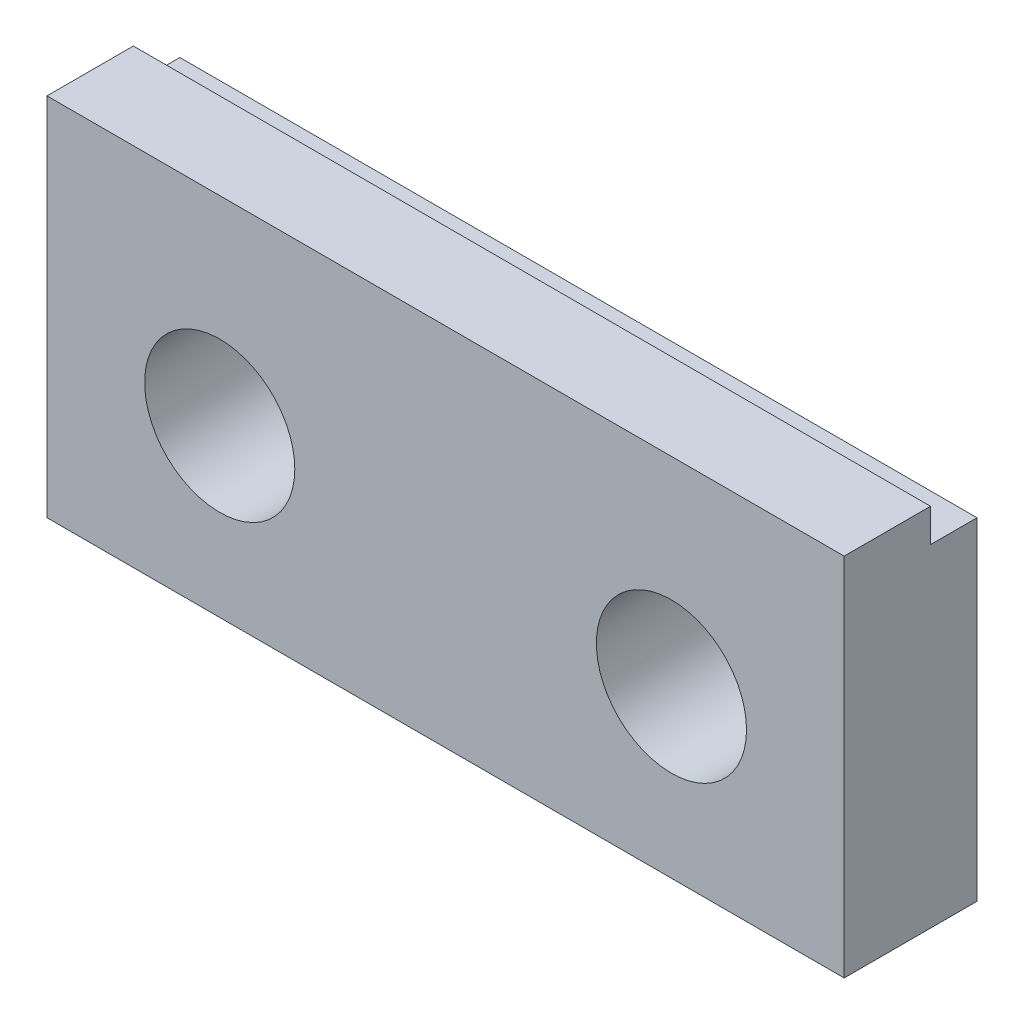
SolidWorks part; units mm, degrees
material "6061-T6 (SS)"
ref_plane "Front" through (0, 0, 0) normal (0, 0, 1) x (1, 0, 0)
ref_plane "Top" through (0, 0, 0) normal (0, 1, 0) x (1, 0, 0)
ref_plane "Right" through (0, 0, 0) normal (1, 0, 0) x (0, 0, -1)
sketch "Sketch1" plane through (0, 0, 0) normal (0, 0, 1) x (1, 0, 0)
  line L1 (-6, 3) -> (6, 3)
  line L2 (-6, 3) -> (-6, -2.5)
  line L3 (-6, -2.5) -> (6, -2.5)
  line L4 (6, 3) -> (6, -2.5)
  dimension "D1" = 6
  dimension "D2" = 6
  dimension "D3" = 3
  dimension "D4" = 2.5
extrude "Extrude1" add sketch "Sketch1" against normal blind 2
sketch "Sketch2" plane through (0, 0, 0) normal (0, 0, 1) x (1, 0, 0)
  circle A0 centre (-3.4, 0) radius 1.1303
  circle A1 centre (3.4, 0) radius 1.1303
  dimension "D3" = 2.2606
  dimension "D4" = 2.2606
  dimension "D1" = 3.4
  dimension "D2" = 3.4
extrude "Extrude2" cut sketch "Sketch2" against normal through all
sketch "Sketch3" plane through (6, 0, 0) normal (1, 0, 0) x (0, 0, -1)
  line L0 (2, -2.5) -> (0, -2.5) construction
  line L1 (2, 3) -> (1.3, 3)
  line L2 (2, 3) -> (2, 2.5)
  line L3 (2, 2.5) -> (1.3, 2.5)
  line L4 (1.3, 3) -> (1.3, 2.5)
  dimension "D1" = 5
  dimension "D2" = 0.7
extrude "Extrude3" cut sketch "Sketch3" against normal through all
